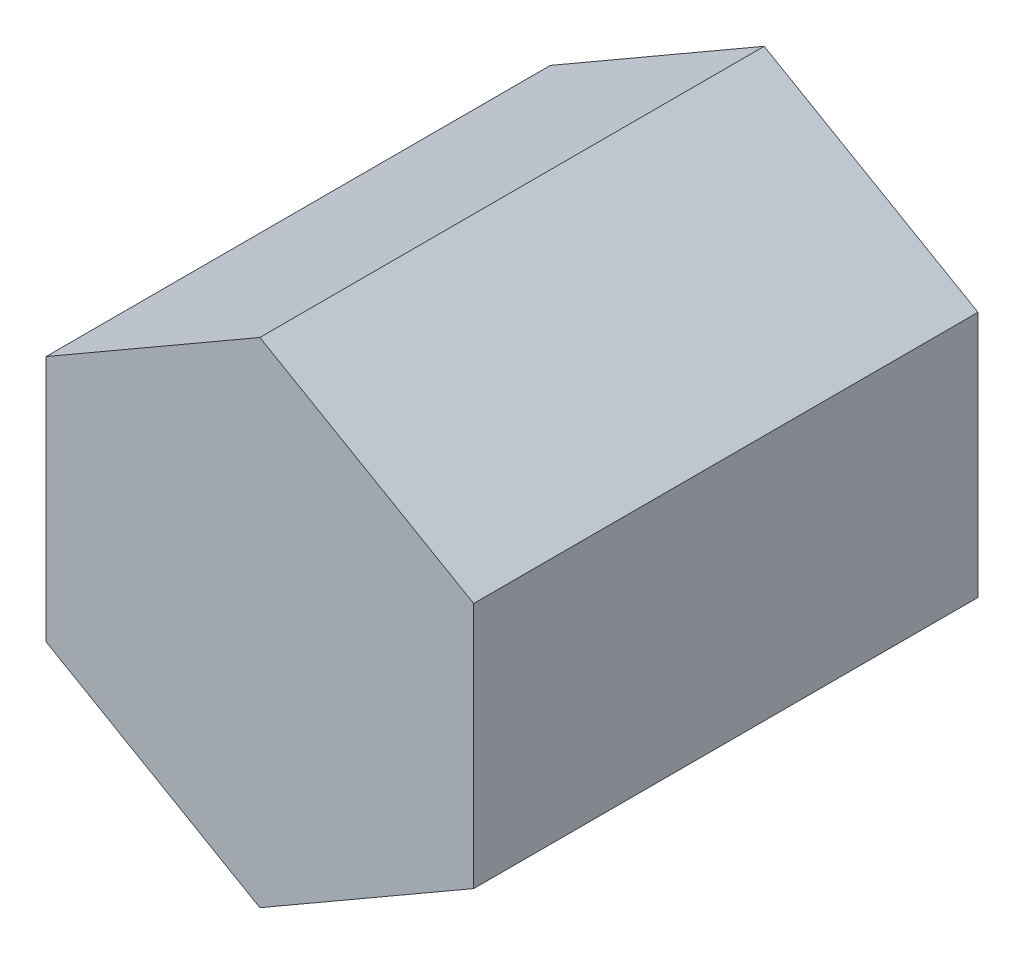
SolidWorks part; units mm, degrees
material "1023 Carbon Steel Sheet (SS)"
ref_plane "Front Plane" through (0, 0, 0) normal (0, 0, 1) x (1, 0, 0)
ref_plane "Top Plane" through (0, 0, 0) normal (0, 1, 0) x (1, 0, 0)
ref_plane "Right Plane" through (0, 0, 0) normal (1, 0, 0) x (0, 0, -1)
sketch "Sketch1" plane through (0, 0, 0) normal (0, 0, 1) x (1, 0, 0)
  line L1 (0, 24.4797) -> (-21.2, 12.2398)
  line L2 (-21.2, 12.2398) -> (-21.2, -12.2398)
  line L3 (-21.2, -12.2398) -> (0, -24.4797)
  line L4 (0, -24.4797) -> (21.2, -12.2398)
  line L5 (21.2, -12.2398) -> (21.2, 12.2398)
  line L6 (21.2, 12.2398) -> (0, 24.4797)
  circle A0 centre (0, 0) radius 21.2 construction
extrude "Boss-Extrude1" add sketch "Sketch1" along normal mid plane 50
